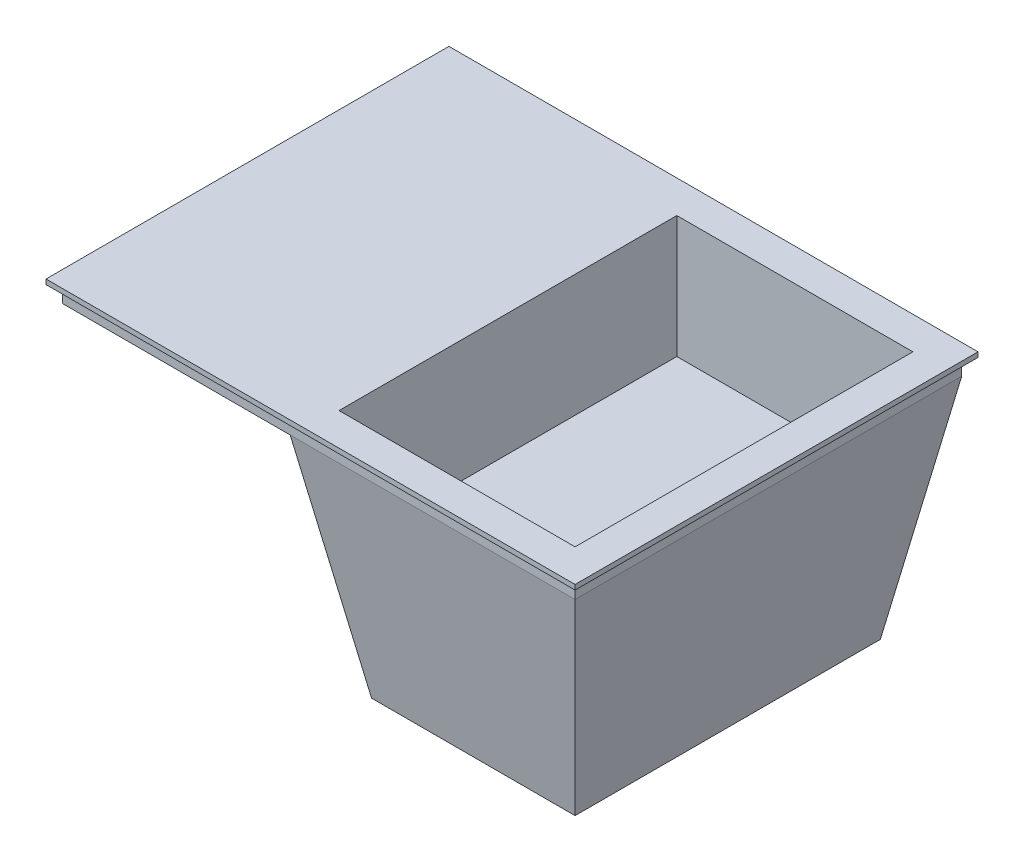
SolidWorks part; units mm, degrees
ref_plane "Спереди" through (0, 0, 0) normal (0, 0, 1) x (1, 0, 0)
ref_plane "Сверху" through (0, 0, 0) normal (0, 1, 0) x (1, 0, 0)
ref_plane "Справа" through (0, 0, 0) normal (1, 0, 0) x (0, 0, -1)
sketch "Эскиз1" plane through (0, 0, 0) normal (0, 1, 0) x (1, 0, 0)
  line L1 (315, -237.5) -> (-315, -237.5)
  line L2 (315, -237.5) -> (315, 237.5)
  line L3 (315, 237.5) -> (-315, 237.5)
  line L4 (-315, -237.5) -> (-315, 237.5)
  line L5 (315, -237.5) -> (-315, 237.5) construction
  line L6 (315, 237.5) -> (-315, -237.5) construction
  point P0 (0, 0)
  dimension "D1" = 475
  dimension "D2" = 630
extrude "Бобышка-Вытянуть1" add sketch "Эскиз1" along normal blind 300
sketch "Эскиз2" plane through (0, 0, 237.5) normal (0, 0, 1) x (1, 0, 0)
  line L1 (-315, 0) -> (15, 0)
  line L2 (-315, 0) -> (-315, 280)
  line L3 (-315, 280) -> (-35, 280)
  line L4 (15, 0) -> (-35, 280)
  line L5 (-315, 300) -> (315, 300) construction
  line L6 (315, 300) -> (315, 0) construction
  line L7 (-315, 0) -> (315, 0) construction
  line L8 (315, 280) -> (265, 0)
  line L9 (265, 0) -> (315, 0)
  line L10 (315, 0) -> (315, 280)
  line L11 (-35, 280) -> (-35, 0) construction
  dimension "D1" = 350
  dimension "D2" = 20
  dimension "D3" = 50
  dimension "D4" = 50
extrude "Вырез-Вытянуть1" cut sketch "Эскиз2" against normal through all both and the other way through all
sketch "Эскиз3" plane through (0, 300, 0) normal (0, 1, 0) x (1, 0, 0)
  line L8 (-325, 247.5) -> (-325, -247.5)
  line L9 (-325, -247.5) -> (325, -247.5)
  line L10 (325, -247.5) -> (325, 247.5)
  line L11 (325, 247.5) -> (-325, 247.5)
  line L12 (-325, 247.5) -> (-325, -247.5)
  line L13 (-325, -247.5) -> (325, -247.5)
  line L14 (325, -247.5) -> (325, 247.5)
  line L15 (325, 247.5) -> (-325, 247.5)
  dimension "D1" = 10
extrude "Бобышка-Вытянуть2" add sketch "Эскиз3" along normal blind 6
sketch "Эскиз4" plane through (315, 0, 0) normal (1, 0, 0) x (0, 0, -1)
  line L0 (-237.5, 280) -> (-187.5, 0)
  line L1 (-187.5, 0) -> (-237.5, 0)
  line L2 (-237.5, 0) -> (-237.5, 280)
  line L3 (237.5, 280) -> (237.5, 0)
  line L4 (237.5, 0) -> (187.5, 0)
  line L5 (187.5, 0) -> (237.5, 280)
  dimension "D1" = 50
extrude "Вырез-Вытянуть2" cut sketch "Эскиз4" against normal through all both and the other way through all
sketch "Эскиз5" plane through (0, 306, 0) normal (0, 1, 0) x (1, 0, 0)
  line L0 (285, -207.5) -> (285, -247.5) construction
  line L1 (-5, -207.5) -> (285, -207.5)
  line L2 (-5, -207.5) -> (-5, 207.5)
  line L3 (-5, 207.5) -> (285, 207.5)
  line L4 (285, -207.5) -> (285, 207.5)
  line L5 (-325, -247.5) -> (325, -247.5) construction
  line L6 (285, 207.5) -> (285, 247.5) construction
  line L7 (325, 247.5) -> (-325, 247.5) construction
  line L8 (285, 207.5) -> (325, 207.5) construction
  line L9 (325, -247.5) -> (325, 247.5) construction
  point P4 (305, 207.5)
  dimension "D1" = 40
  dimension "D2" = 290
extrude "Вырез-Вытянуть4" cut sketch "Эскиз5" against normal blind 150
